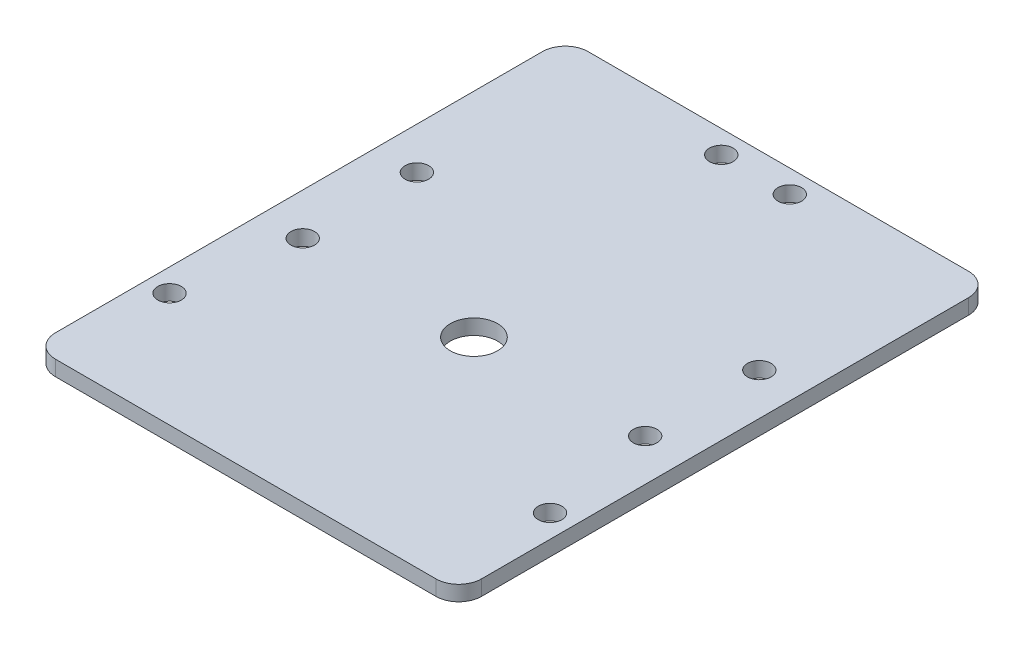
SolidWorks part; units mm, degrees
material "Thornel Mat VMA"
ref_plane "Front Plane" through (0, 0, 0) normal (0, 0, 1) x (1, 0, 0)
ref_plane "Top Plane" through (0, 0, 0) normal (0, 1, 0) x (1, 0, 0)
ref_plane "Right Plane" through (0, 0, 0) normal (1, 0, 0) x (0, 0, -1)
sketch "Sketch1" plane through (0, 0, 0) normal (0, 1, 0) x (1, 0, 0)
  line L0 (-4.5, 32) -> (4.5, 32)
  line L1 (-28, 35) -> (28, 35)
  line L2 (-28, 35) -> (-28, -35)
  line L3 (-28, -35) -> (28, -35)
  line L4 (28, 35) -> (28, -35)
  line L5 (-28, 35) -> (28, -35) construction
  line L6 (-28, -35) -> (28, 35) construction
  circle A0 centre (-22.5, -5) radius 1.55
  circle A1 centre (22.5, -5) radius 1.55
  circle A2 centre (-4.5, 32) radius 1.55
  circle A3 centre (4.5, 32) radius 1.55
  circle A4 centre (-22.5, 10) radius 1.55
  circle A5 centre (22.5, 10) radius 1.55
  circle A6 centre (-25, -20) radius 1.55
  circle A7 centre (25, -20) radius 1.55
  circle A8 centre (0, -5) radius 3.1
  point P0 (0, 0)
  point P13 (0, 32)
  point P25 (0, 0)
  point P26 (0, 0)
  dimension "D1" = 3.1
  dimension "D2" = 56
  dimension "D9" = 25
  dimension "D10" = 3.1
  dimension "D11" = 3.1
  dimension "D12" = 3.1
  dimension "D13" = 3.1
  dimension "D17" = 6.2
  dimension "D3" = 22.5
  dimension "D4" = 3
  dimension "D5" = 40
  dimension "D6" = 45
  dimension "D7" = 70
  dimension "D8" = 9
  dimension "D14" = 50
  dimension "D15" = 25
  dimension "D16" = 55
extrude "Boss-Extrude1" add sketch "Sketch1" along normal blind 2
fillet "Fillet1" radius 3 4 edges at (28, 1, 35) (28, 1, -35) (-28, 1, -35) (-28, 1, 35)
